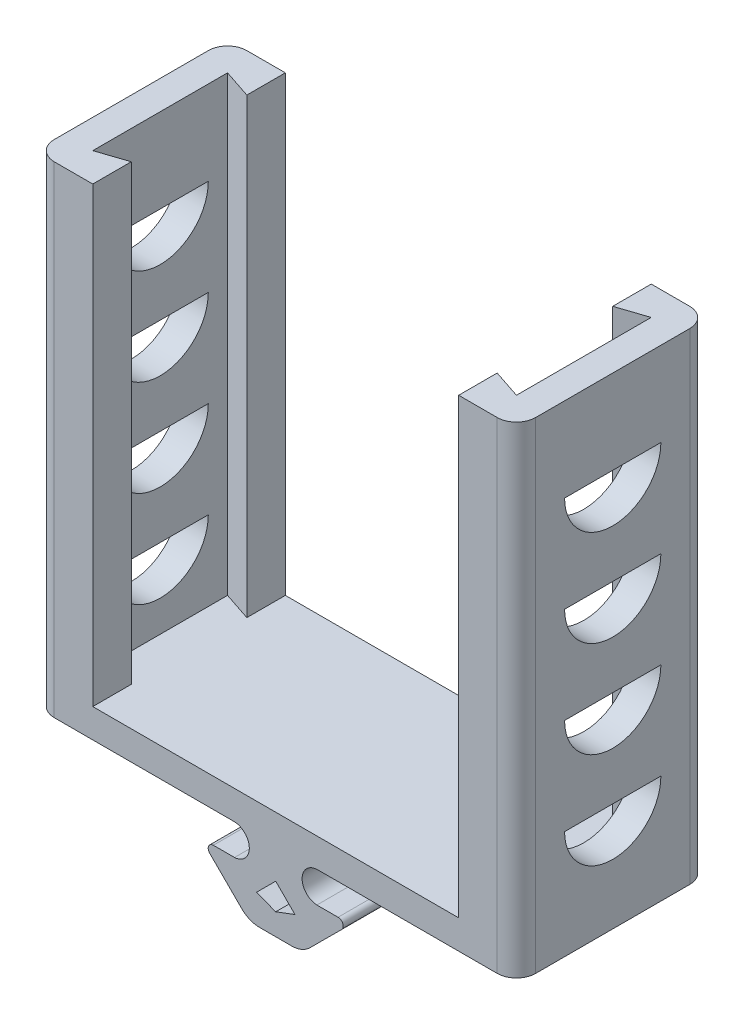
SolidWorks part; units mm, degrees
ref_plane "Front Plane" through (0, 0, 0) normal (0, 0, 1) x (1, 0, 0)
ref_plane "Top Plane" through (0, 0, 0) normal (0, 1, 0) x (1, 0, 0)
ref_plane "Right Plane" through (0, 0, 0) normal (1, 0, 0) x (0, 0, -1)
sketch "Sketch1" plane through (0, 0, 0) normal (0, 0, 1) x (1, 0, 0)
  line L0 (-4.2875, 5.9944) -> (-6.4768, 5.9944) construction
  line L1 (0, 0) -> (0, -5.1481) construction
  line L2 (-7.207, 4.2286) -> (-3.8983, 0.9274) construction
  line L4 (-1.6558, 0) -> (0, 0) construction
  line L5 (-4.2749, 5.4944) -> (-6.4768, 5.4944)
  line L6 (-6.8539, 4.5825) -> (-3.5451, 1.2813)
  line L7 (-1.6558, 0.5) -> (0, 0.5)
  line L8 (0, 0.5) -> (0, 8.7042)
  line L9 (-5.4283, 8.7042) -> (-4.4089, 8.7042) construction
  line L10 (-5.4283, 8.2042) -> (-4.3987, 8.2042) construction
  line L11 (-4.4089, 8.7042) -> (0, 8.7042)
  arc A0 (-4.3987, 8.2042) -> (-4.2875, 5.9944) centre (-4.3489, 7.099) cw construction
  arc A1 (-7.207, 4.2286) -> (-6.4768, 5.9944) centre (-6.4768, 4.9605) cw construction
  arc A2 (-3.8983, 0.9274) -> (-1.6558, 0) centre (-1.6558, 3.175) ccw construction
  arc A3 (-4.4089, 8.7042) -> (-4.2749, 5.4944) centre (-4.3489, 7.099) cw
  arc A4 (-6.8539, 4.5825) -> (-6.4768, 5.4944) centre (-6.4768, 4.9605) cw
  arc A5 (-3.5451, 1.2813) -> (-1.6558, 0.5) centre (-1.6558, 3.175) ccw
  dimension "D2" = 1.1063
  dimension "D3" = 1.0339
  dimension "D5" = 3.175
  dimension "D10" = 0.5
  dimension "D1" = 4.674
  dimension "D4" = 2.1893
  dimension "D6" = 1.6558
  dimension "D7" = 5.9944
  dimension "D8" = 2.2098
  dimension "D9" = 1.0296
extrude "Boss-Extrude1" add sketch "Sketch1" along normal blind 20 contours L6 A5 L7 L8 L11 A3 L5 A4
sketch "Sketch2" plane through (0, 8.7042, 0) normal (0, 1, 0) x (1, 0, 0)
  line L1 (0, -20) -> (-23, -20)
  line L2 (0, -20) -> (0, 0)
  line L3 (0, 0) -> (-23, 0)
  line L4 (-25, -18) -> (-25, -2)
  arc A0 (-23, 0) -> (-25, -2) centre (-23, -2) ccw
  arc A1 (-23, -20) -> (-25, -18) centre (-23, -18) cw
  point P9 (-25, -20)
  dimension "D2" = 2
  dimension "D1" = 25
extrude "Boss-Extrude2" add sketch "Sketch2" along normal blind 50
sketch "Sketch4" plane through (0, 58.7042, 0) normal (0, 1, 0) x (1, 0, 0)
  line L1 (-23, -20) -> (0, -20) construction
  line L3 (-22, -17) -> (-22, -3)
  line L7 (0, -20) -> (-19, -20)
  line L9 (-19, -4) -> (-19, 0)
  line L10 (-22, -3) -> (-19, -4)
  line L11 (-19, 0) -> (0, 0)
  line L12 (0, 0) -> (0, -20)
  line L13 (-22, -17) -> (-19, -16)
  line L14 (-19, -16) -> (-19, -20)
  dimension "D4" = 19
extrude "Cut-Extrude1" cut sketch "Sketch4" against normal offset from surface (47 mm away) 3 up to face at (-17.5677, 8.7042, 10)
sketch "Sketch6" plane through (-22, 0, 0) normal (1, 0, 0) x (0, 0, -1)
  line L3 (-15, 19.9542) -> (-5, 19.9542)
  line L7 (-2, 8.7042) -> (-18, 8.7042) construction
  line L8 (-17, 11.7042) -> (-3, 11.7042) construction
  arc A0 (-5, 19.9542) -> (-15, 19.9542) centre (-10, 19.9542) cw
  point P7 (-10, 11.7042)
  dimension "D1" = 5
  dimension "D2" = 11.25
extrude "Cut-Extrude2" cut sketch "Sketch6" against normal through all
pattern_linear "LPattern1" count 4 spacing 10 along (0, 1, 0) of "Cut-Extrude2"
mirror "Mirror2" of "Boss-Extrude1", "Boss-Extrude2", "Cut-Extrude1", "LPattern1", "Cut-Extrude2"
sketch "Sketch7" plane through (0, 0, 20) normal (0, 0, 1) x (1, 0, 0)
  line L5 (-2, 3.5) -> (0, 5.5)
  line L6 (0, 5.5) -> (2, 3.5)
  line L8 (-2, 3.5) -> (0, 2.75)
  line L9 (0, 2.75) -> (2, 3.5)
extrude "Cut-Extrude3" cut sketch "Sketch7" against normal blind 30
